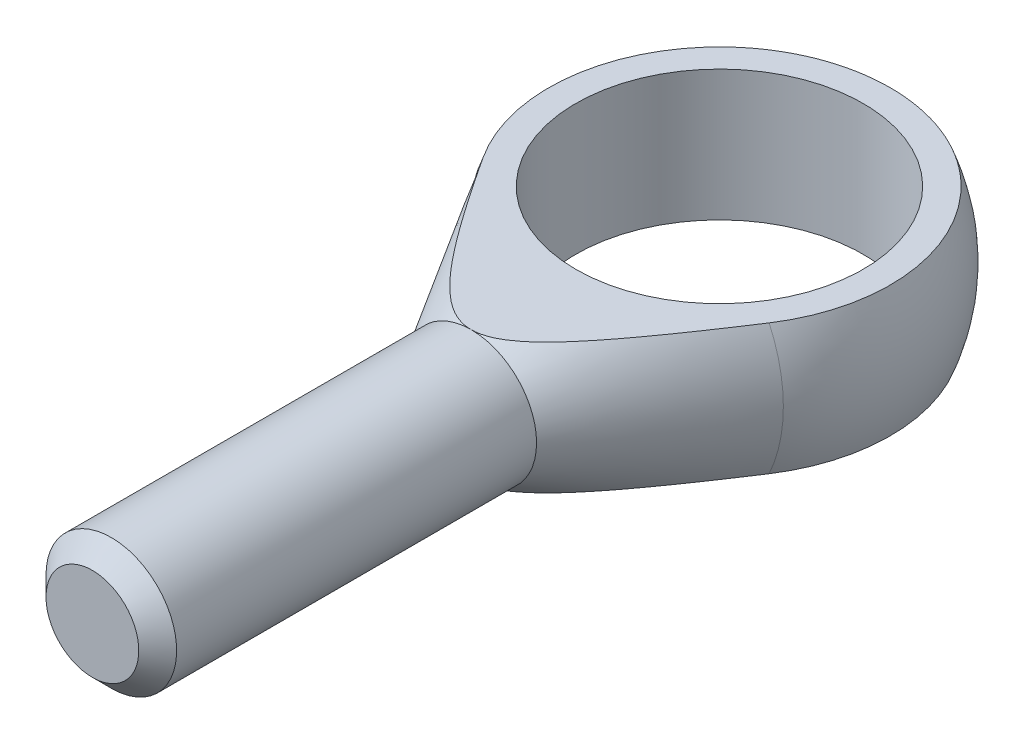
SolidWorks part; units mm, degrees
material "1.0545 (S355N)"
ref_plane "Płaszczyzna przednia" through (0, 0, 0) normal (0, 0, 1) x (1, 0, 0)
ref_plane "Płaszczyzna górna" through (0, 0, 0) normal (0, 1, 0) x (1, 0, 0)
ref_plane "Płaszczyzna prawa" through (0, 0, 0) normal (1, 0, 0) x (0, 0, -1)
sketch "Szkic1" plane through (0, 0, 0) normal (0, 1, 0) x (1, 0, 0)
  line L0 (0, 26.0435) -> (0, -71.4286) construction
  line L1 (-5, -48) -> (5, -48)
  line L2 (5, -48) -> (5, -19)
  line L3 (-5, -48) -> (-5, -19)
  line L4 (-12.0377, -7.148) -> (-5, -19)
  line L5 (5, -19) -> (12.0377, -7.148)
  line L6 (-5, -19) -> (5, -19)
  line L7 (0, 14) -> (0, -48)
  arc A0 (12.0377, -7.148) -> (-12.0377, -7.148) centre (0, 0) ccw
  point P7 (0, -48)
  dimension "d4" = 28
  dimension "d2" = 10
  dimension "l1" = 48
  dimension "l3" = 29
revolve "Obrót1" add sketch "Szkic1" angle 360 about L0
sketch "Szkic2" plane through (0, 0, 0) normal (1, 0, 0) x (0, 0, -1)
  line L4 (-19, 5) -> (13.0767, 5)
  line L5 (-19, -5) -> (13.0767, -5)
  line L6 (-19, -5) -> (-7.148, -12.0377) construction
  line L7 (-7.148, 12.0377) -> (-19, 5) construction
  line L8 (-19, -5) -> (-7.148, -12.0377)
  line L9 (-7.148, 12.0377) -> (-19, 5)
  arc A0 (-7.148, -12.0377) -> (-7.148, 12.0377) centre (0, 0) ccw construction
  arc A1 (-7.148, -12.0377) -> (13.0767, -5) centre (0, 0) ccw
  arc A2 (13.0767, 5) -> (-7.148, 12.0377) centre (0, 0) ccw
extrude "Wytnij-wyciągnięcie1" cut sketch "Szkic2" against normal through all both and the other way through all
sketch "Szkic3" plane through (0, 0, 0) normal (0, 1, 0) x (1, 0, 0)
  circle A0 centre (0, 0) radius 11
  dimension "b" = 22
extrude "Wytnij-wyciągnięcie2" cut sketch "Szkic3" against normal through all both and the other way through all contours A0
chamfer "Sfazowanie1" distance 1.45 angle 45 1 edges at (-5, 0, 48)
equation "\"D1@Sfazowanie1\"=\"l3@Szkic1\"*0.05"
